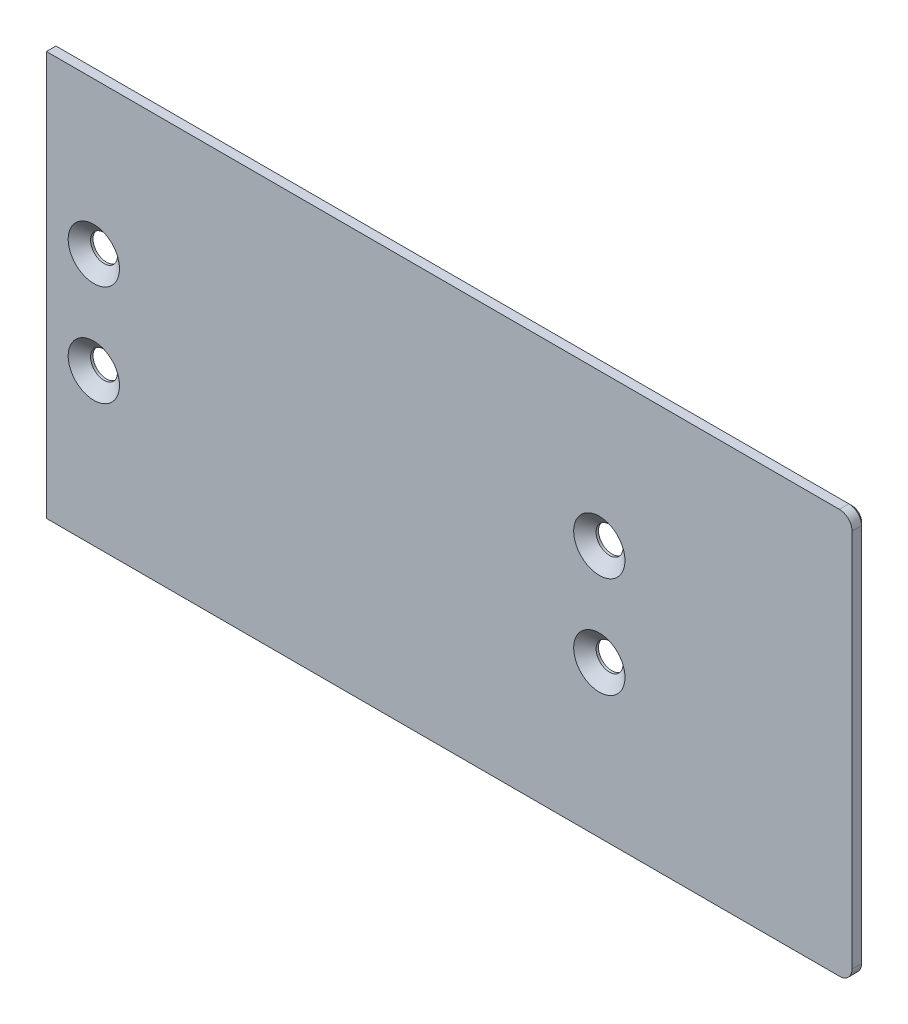
SolidWorks part; units mm, degrees
ref_plane "Front Plane" through (0, 0, 0) normal (0, 0, 1) x (1, 0, 0)
ref_plane "Top Plane" through (0, 0, 0) normal (0, 1, 0) x (1, 0, 0)
ref_plane "Right Plane" through (0, 0, 0) normal (1, 0, 0) x (0, 0, -1)
sketch "Sketch1" plane through (0, 0, 0) normal (0, 1, 0) x (1, 0, 0)
  line L1 (0, 0) -> (202.4062, 0)
  line L2 (0, 0) -> (0, -3.175)
  line L3 (0, -3.175) -> (202.4062, -3.175)
  line L4 (202.4062, 0) -> (202.4062, -3.175)
  dimension "D1" = 202.4062
  dimension "D2" = 3.175
extrude "Boss-Extrude1" add sketch "Sketch1" against normal blind 101.6
sketch "Sketch13" plane through (0, 0, 3.175) normal (0, 0, 1) x (1, 0, 0)
  line L0 (0, -50.8) -> (202.4062, -50.8) construction
  line L1 (0, -101.6) -> (0, 0) construction
  line L2 (202.4062, -101.6) -> (202.4062, 0) construction
  line L3 (11.9062, 0) -> (11.9062, -101.6) construction
  line L4 (138.9062, 0) -> (138.9062, -101.6) construction
  line L5 (0, 0) -> (202.4062, 0) construction
  line L6 (0, -101.6) -> (202.4062, -101.6) construction
  dimension "D1" = 11.9062
  dimension "D2" = 63.5
hole_wizard "CSK for 1/4 Flat Head Machine Screw (100)5" positions "Sketch14" profile "Sketch15" countersink size "1/4" standard "ANSI Inch" end condition through all
sketch "Sketch14" plane through (0, 0, 3.175) normal (0, 0, 1) x (1, 0, 0)
  line L0 (11.9062, 0) -> (11.9062, -101.6) construction
  line L1 (0, -50.8) -> (202.4062, -50.8) construction
  line L2 (138.9062, 0) -> (138.9062, -101.6) construction
  point P0 (11.9062, -38.1)
  point P2 (11.9062, -63.5)
  point P4 (138.9062, -63.5)
  point P6 (138.9062, -38.1)
  dimension "D1" = 0
  dimension "D2" = 12.7
  dimension "D3" = 0
  dimension "D4" = 12.7
  dimension "D5" = 0
  dimension "D6" = 12.7
  dimension "D7" = 0
  dimension "D8" = 12.7
sketch "Sketch15" plane through (11.9062, -38.1, 3.175) normal (1, 0, 0) x (0, -1, 0)
  line L0 (0, 0) -> (0, 3.175)
  line L1 (0, 3.175) -> (3.3782, 3.175)
  line L2 (3.3782, 3.175) -> (3.3782, 2.5682)
  line L3 (3.3782, 2.5682) -> (6.4389, 0)
  line L5 (6.4389, 0) -> (0, 0)
  line L6 (-3.3782, 2.5682) -> (-6.4389, 0) construction
  line L11 (0, -6.35) -> (0, 107.95) construction
  dimension "Thru Hole Dia." = 6.7564
  dimension "Thru Hole Depth" = 3.175
  dimension "Near C'Sink Dia." = 12.8778
  dimension "Near C'Sink Angle" = 100
sketch "Sketch17" plane through (0, 0, 3.175) normal (0, 0, 1) x (1, 0, 0)
  line L4 (0, 0) -> (202.4062, 0) construction
  line L5 (202.4062, -3.175) -> (202.4062, 0)
  line L6 (202.4062, 0) -> (199.2312, 0)
  line L7 (202.4062, -50.8) -> (229.7462, -50.8) construction
  line L8 (202.4062, -101.6) -> (202.4062, 0) construction
  line L9 (202.4062, -98.425) -> (202.4062, -101.6)
  line L10 (202.4062, -101.6) -> (199.2312, -101.6)
  arc A1 (202.4062, -3.175) -> (199.2312, 0) centre (199.2312, -3.175) ccw
  arc A2 (202.4062, -98.425) -> (199.2312, -101.6) centre (199.2312, -98.425) cw
  dimension "D1" = 3.175
  dimension "D2" = 3.175
extrude "Cut-Extrude1" cut sketch "Sketch17" against normal through all
chamfer "Chamfer1" distance 0.7874 angle 45 6 edges at (202.4062, -50.8, 0) (201.4763, -0.9299, 0) (201.4763, -100.6701, 0) (99.6156, 0, 0) (0, -50.8, 0) (99.6156, -101.6, 0)
